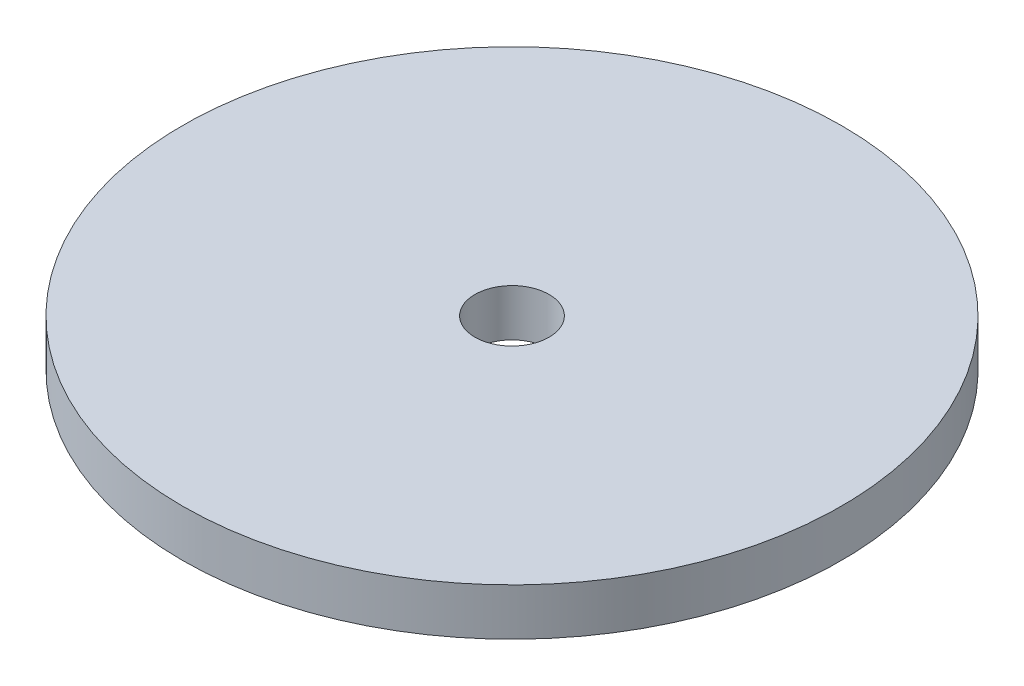
SolidWorks part; units mm, degrees
material "Ceramic Porcelain"
ref_plane "Front Plane" through (0, 0, 0) normal (0, 0, 1) x (1, 0, 0)
ref_plane "Top Plane" through (0, 0, 0) normal (0, 1, 0) x (1, 0, 0)
ref_plane "Right Plane" through (0, 0, 0) normal (1, 0, 0) x (0, 0, -1)
sketch "Sketch1" plane through (0, 0, 0) normal (0, 1, 0) x (1, 0, 0)
  circle A0 centre (0, 0) radius 5
  circle A1 centre (0, 0) radius 44.45
  dimension "D1" = 10
  dimension "D2" = 88.9
extrude "Boss-Extrude1" add sketch "Sketch1" along normal blind 6.35
